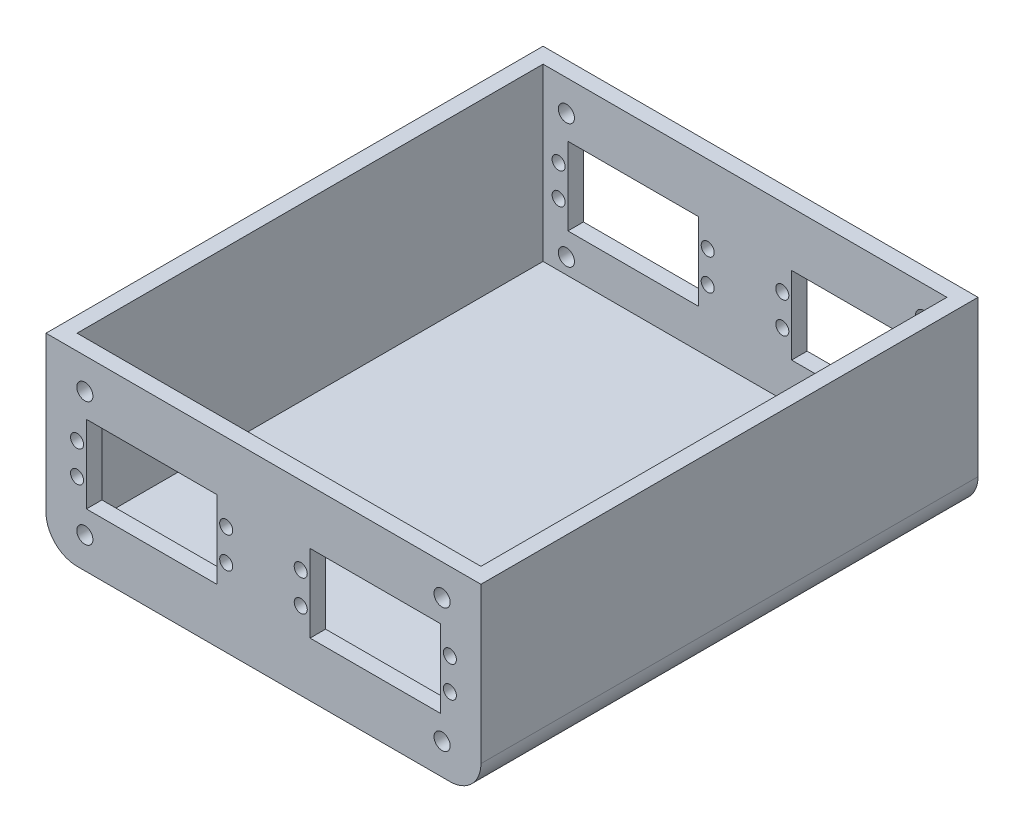
SolidWorks part; units mm, degrees
ref_plane "Front Plane" through (0, 0, 0) normal (0, 0, 1) x (1, 0, 0)
ref_plane "Top Plane" through (0, 0, 0) normal (0, 1, 0) x (1, 0, 0)
ref_plane "Right Plane" through (0, 0, 0) normal (1, 0, 0) x (0, 0, -1)
sketch "Sketch1" plane through (0, 0, 0) normal (0, 0, 1) x (1, 0, 0)
  line L1 (0, 0) -> (-140, 0)
  line L2 (0, 0) -> (0, 60)
  line L3 (0, 60) -> (-140, 60)
  line L4 (-140, 0) -> (-140, 60)
  dimension "D1" = 140
  dimension "D2" = 60
extrude "Boss-Extrude1" add sketch "Sketch1" along normal blind 160
shell "Shell1" thickness 5
sketch "Sketch2" plane through (0, 0, 160) normal (0, 0, 1) x (1, 0, 0)
  line L0 (-140, 30) -> (0, 30) construction
  line L1 (-140, 60) -> (-140, 0) construction
  line L2 (0, 0) -> (0, 60) construction
  line L3 (-70, 60) -> (-70, 0) construction
  line L4 (0, 60) -> (-140, 60) construction
  line L5 (-140, 0) -> (0, 0) construction
  line L6 (-106, 42.5) -> (-106, 17.5) construction
  line L7 (-127, 42.5) -> (-85, 42.5)
  line L8 (-127, 42.5) -> (-127, 17.5)
  line L9 (-127, 17.5) -> (-85, 17.5)
  line L10 (-85, 42.5) -> (-85, 17.5)
  line L11 (-13, 17.5) -> (-55, 17.5)
  line L12 (-55, 42.5) -> (-55, 17.5)
  line L13 (-13, 42.5) -> (-55, 42.5)
  line L14 (-13, 42.5) -> (-13, 17.5)
  circle A0 centre (-127.5, 50) radius 2.6
  circle A1 centre (-127.5, 10) radius 2.6
  circle A2 centre (-12.5, 10) radius 2.6
  circle A3 centre (-12.5, 50) radius 2.6
  circle A4 centre (-130, 35) radius 2.1
  circle A5 centre (-130, 25) radius 2.1
  circle A6 centre (-82, 25) radius 2.1
  circle A7 centre (-82, 35) radius 2.1
  circle A8 centre (-58, 25) radius 2.1
  circle A9 centre (-58, 35) radius 2.1
  circle A10 centre (-10, 25) radius 2.1
  circle A11 centre (-10, 35) radius 2.1
  dimension "D2" = 5.2
  dimension "D5" = 4.2
  dimension "D8" = 4.2
  dimension "D1" = 10
  dimension "D3" = 12.5
  dimension "D4" = 42
  dimension "D6" = 10
  dimension "D7" = 3
  dimension "D9" = 10
  dimension "D10" = 7.5
  dimension "D11" = 7.5
  dimension "D12" = 10
  dimension "D13" = 5
extrude "Cut-Extrude1" cut sketch "Sketch2" against normal through all
fillet "Fillet1" radius 10 2 edges at (-140, 0, 80) (0, 0, 80)
